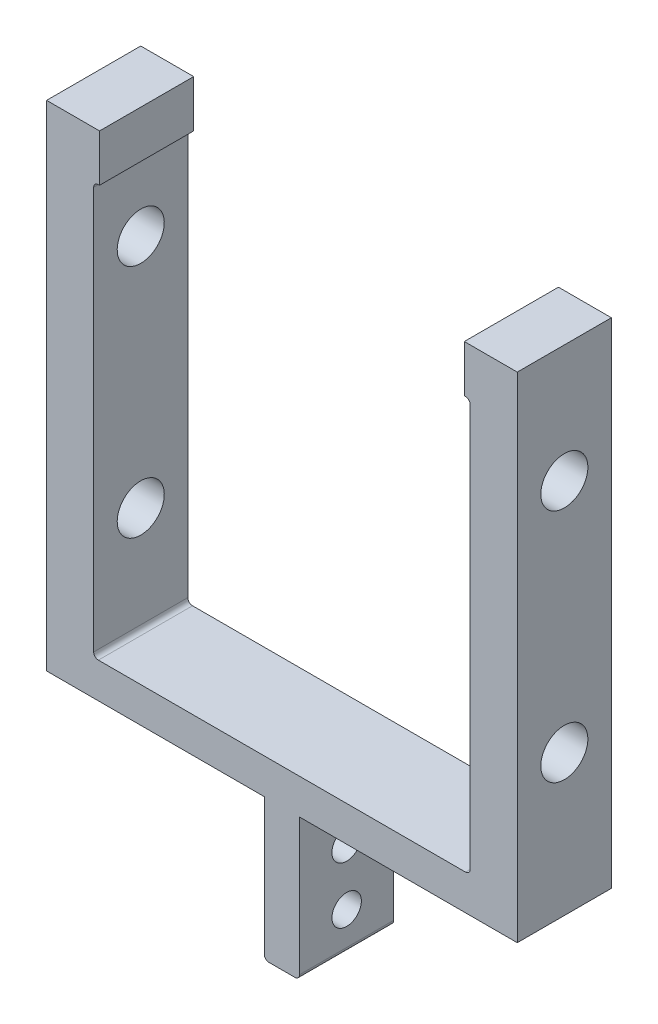
SolidWorks part; units mm, degrees
material "6061 Alloy"
ref_plane "Front Plane" through (0, 0, 0) normal (0, 0, 1) x (1, 0, 0)
ref_plane "Top Plane" through (0, 0, 0) normal (0, 1, 0) x (1, 0, 0)
ref_plane "Right Plane" through (0, 0, 0) normal (1, 0, 0) x (0, 0, -1)
sketch "Sketch1" plane through (0, 0, 0) normal (0, 0, 1) x (1, 0, 0)
  line L7 (4.7625, 0) -> (-4.7625, 0)
  line L13 (-4.7625, 0) -> (-4.7625, 38.1)
  line L14 (-4.7625, 38.1) -> (-63.5, 38.1)
  line L15 (-63.5, 38.1) -> (-63.5, 171.45)
  line L17 (-50.8, 158.75) -> (-50.8, 47.625)
  line L18 (-50.8, 47.625) -> (50.8, 47.625)
  line L19 (0, 47.625) -> (0, 0) construction
  line L20 (50.8, 158.75) -> (50.8, 47.625)
  line L22 (63.5, 38.1) -> (63.5, 171.45)
  line L23 (4.7625, 38.1) -> (63.5, 38.1)
  line L24 (4.7625, 0) -> (4.7625, 38.1)
  line L26 (63.5, 171.45) -> (49.2125, 171.45)
  line L29 (50.8, 158.75) -> (49.2125, 158.75)
  line L30 (49.2125, 171.45) -> (49.2125, 158.75)
  line L31 (-49.2125, 158.75) -> (-49.2125, 171.45)
  line L32 (-49.2125, 158.75) -> (-50.8, 158.75)
  line L33 (49.2125, 158.75) -> (-49.2125, 158.75) construction
  line L34 (-49.2125, 171.45) -> (-63.5, 171.45)
  line L35 (49.2125, 171.45) -> (-49.2125, 171.45) construction
  line L36 (0, -55) -> (0, 55) construction
  line L37 (50.8, 158.75) -> (63.5, 158.75) construction
  point P12 (0, 47.625)
  point P17 (0, 0)
  point P24 (0, 171.45)
  dimension "D1" = 9.525
  dimension "D2" = 101.6
  dimension "D3" = 38.1
  dimension "D5" = 9.525
  dimension "D8" = 133.35
  dimension "D7" = 98.425
  dimension "D4" = 12.7
extrude "Boss-Extrude1" add sketch "Sketch1" along normal mid plane 25.4
sketch "Sketch2" plane through (-63.5, 0, 0) normal (-1, 0, 0) x (0, 0, 1)
  line L0 (-26.0251, 0) -> (40.3307, 0) construction
  line L1 (0, 127) -> (0, 0) construction
  circle A0 centre (0, 76.2) radius 6.35
  circle A1 centre (0, 139.7) radius 6.35
  dimension "D2" = 12.7
  dimension "D1" = 12.7
  dimension "D4" = 63.5
  dimension "D3" = 76.2
extrude "Cut-Extrude1" cut sketch "Sketch2" against normal through all
fillet "Fillet1" radius 1.27 6 edges at (-50.8, 47.625, 0) (50.8, 47.625, 0) (50.8, 158.75, 0) (-4.7625, 0, 0) (4.7625, 0, 0) (-50.8, 158.75, 0)
hole_wizard "Hole1" positions "Sketch15" profile "Sketch16" legacy end condition through all
sketch "Sketch15" plane through (4.7625, 0, 0) normal (-1, 0, 0) x (0, 0, 1)
  line L0 (0, -69.85) -> (0, 69.85) construction
  line L1 (-12.7, 0) -> (12.7, 0) construction
  point P0 (0, 25.4)
  point P3 (0, 10.16)
  dimension "D1" = 10.16
  dimension "D2" = 15.24
sketch "Sketch16" plane through (4.7625, 25.4, 0) normal (0, 1, 0) x (0, 0, -1)
  line L0 (0, 0) -> (0, 70.6495)
  line L1 (0, 70.6495) -> (3.9726, 68.2625)
  line L2 (3.9726, 68.2625) -> (3.9726, 0)
  line L4 (3.9726, 0) -> (0, 0)
  line L6 (0, 70.6495) -> (-3.9726, 68.2625) construction
  line L7 (0, -4.2442) -> (0, 117.3081) construction
  dimension "Diameter" = 7.9451
  dimension "Depth" = 68.2625
  dimension "Drill Angle" = 118
equation "\"BoomDistance\"=2.5"
equation "\"D4@Sketch2\"= \"BoomDistance\""
equation "\"D7@Sketch1\"=\"D2@Sketch1\"-.125"
equation "\"yokewidth\"=4"
equation "\"D2@Sketch1\"= \"yokewidth\""
equation "\"Pillow_Block_Width\"= 1"
equation "\"D1@Boss-Extrude1\"=\"Pillow_Block_Width\""
